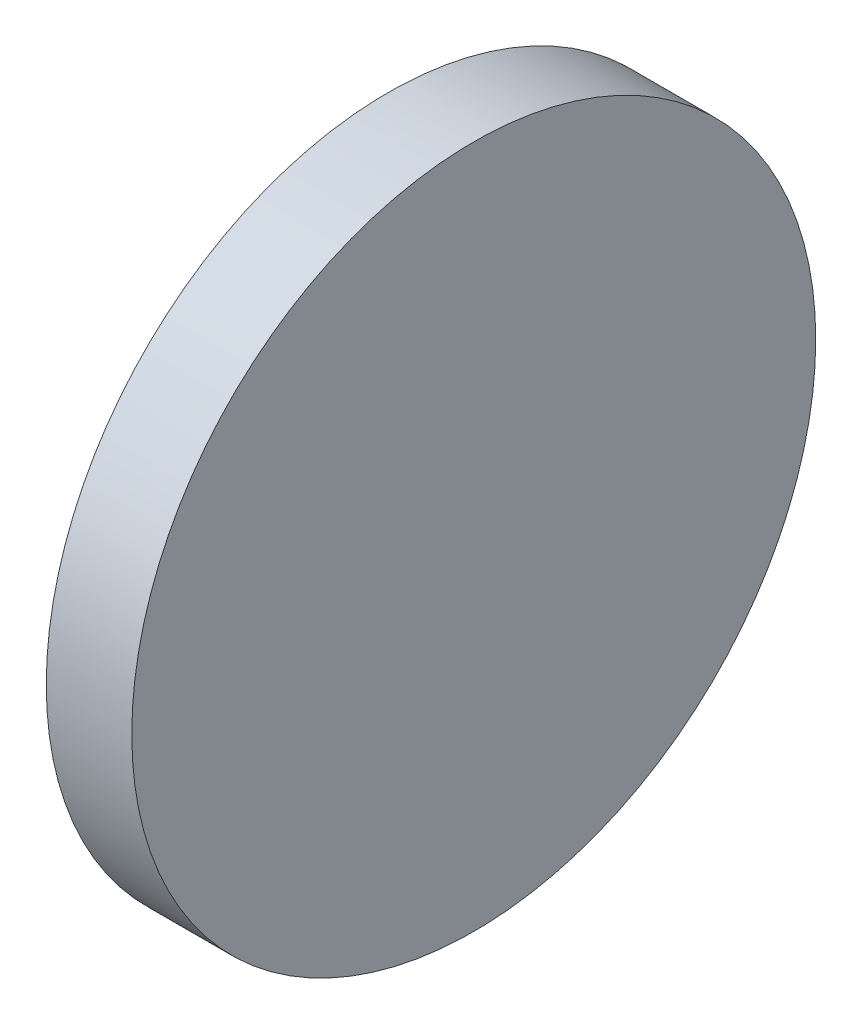
SolidWorks part; units mm, degrees
ref_plane "Front Plane" through (0, 0, 0) normal (0, 0, 1) x (1, 0, 0)
ref_plane "Top Plane" through (0, 0, 0) normal (0, 1, 0) x (1, 0, 0)
ref_plane "Right Plane" through (0, 0, 0) normal (1, 0, 0) x (0, 0, -1)
sketch "Sketch1" plane through (0, 0, 0) normal (1, 0, 0) x (0, 0, -1)
  circle A0 centre (0, 0) radius 20
  dimension "D1" = 40
extrude "Boss-Extrude1" add sketch "Sketch1" along normal blind 5
